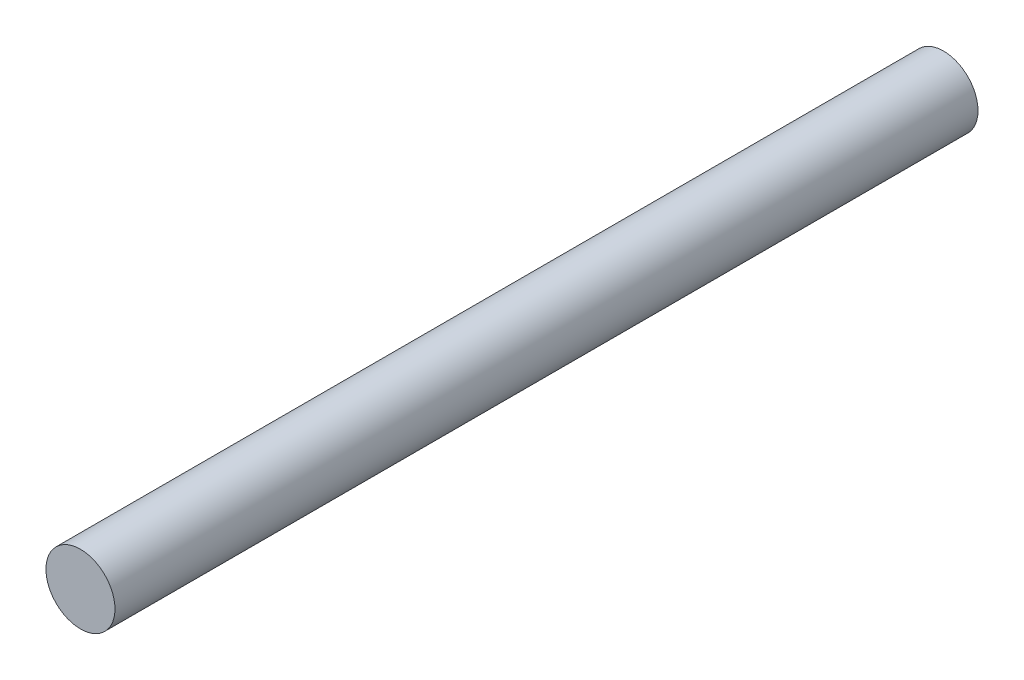
SolidWorks part; units mm, degrees
ref_plane "前视基准面" through (0, 0, 0) normal (0, 0, 1) x (1, 0, 0)
ref_plane "上视基准面" through (0, 0, 0) normal (0, 1, 0) x (1, 0, 0)
ref_plane "右视基准面" through (0, 0, 0) normal (1, 0, 0) x (0, 0, -1)
sketch "草图1" plane through (0, 0, 0) normal (0, 0, 1) x (1, 0, 0)
  circle A0 centre (0, 0) radius 4
  dimension "D1" = 8
extrude "凸台-拉伸1" add sketch "草图1" along normal blind 100
